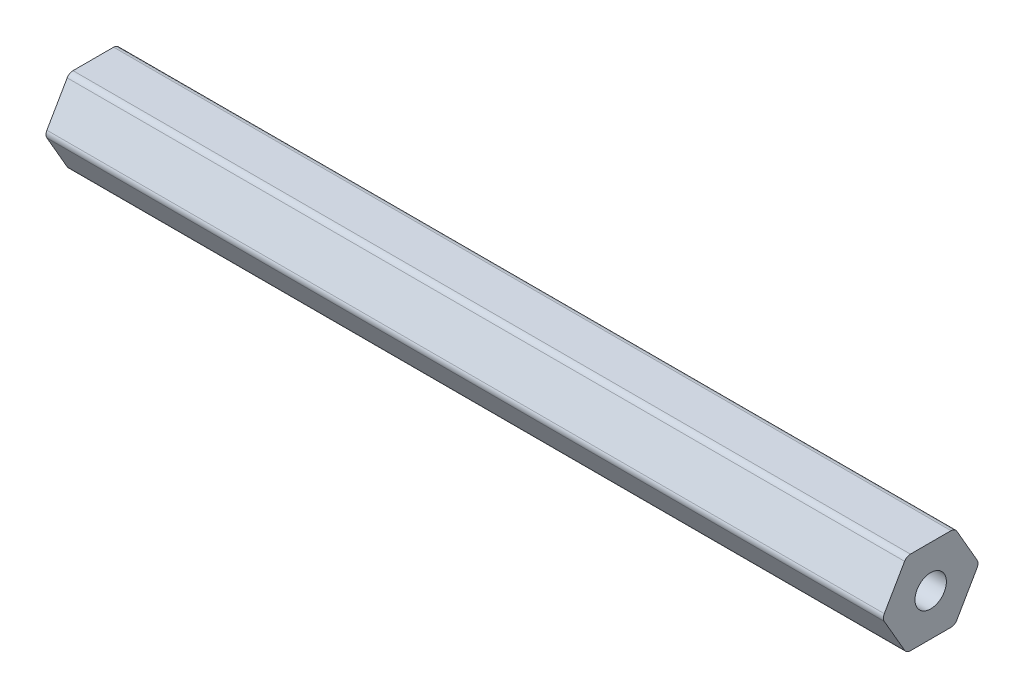
SolidWorks part; units mm, degrees
material "7075-T6 (SN)"
ref_plane "Front Plane" through (0, 0, 0) normal (0, 0, 1) x (1, 0, 0)
ref_plane "Top Plane" through (0, 0, 0) normal (0, 1, 0) x (1, 0, 0)
ref_plane "Right Plane" through (0, 0, 0) normal (1, 0, 0) x (0, 0, -1)
sketch "Sketch1" plane through (0, 0, 0) normal (1, 0, 0) x (0, 0, -1)
  line L1 (7.0391, 0.508) -> (3.9595, 5.842)
  line L2 (3.0796, 6.35) -> (-3.0796, 6.35)
  line L3 (-3.9595, 5.842) -> (-7.0391, 0.508)
  line L4 (-7.0391, -0.508) -> (-3.9595, -5.842)
  line L5 (-3.0796, -6.35) -> (3.0796, -6.35)
  line L6 (3.9595, -5.842) -> (7.0391, -0.508)
  circle A0 centre (0, 0) radius 6.35 construction
  arc A1 (3.0796, 6.35) -> (3.9595, 5.842) centre (3.0796, 5.334) cw
  arc A2 (7.0391, 0.508) -> (7.0391, -0.508) centre (6.1592, 0) cw
  arc A3 (3.9595, -5.842) -> (3.0796, -6.35) centre (3.0796, -5.334) cw
  arc A4 (-3.0796, -6.35) -> (-3.9595, -5.842) centre (-3.0796, -5.334) cw
  arc A5 (-7.0391, -0.508) -> (-7.0391, 0.508) centre (-6.1592, 0) cw
  arc A6 (-3.9595, 5.842) -> (-3.0796, 6.35) centre (-3.0796, 5.334) cw
  circle A7 centre (0, 0) radius 2.3813
  point P11 (3.6662, 6.35)
  point P14 (7.3323, 0)
  dimension "D1" = 12.7
  dimension "D3" = 1.016
  dimension "D4" = 4.7625
  dimension "D2" = 6.35
extrude "Boss-Extrude1" add sketch "Sketch1" along normal blind 127
